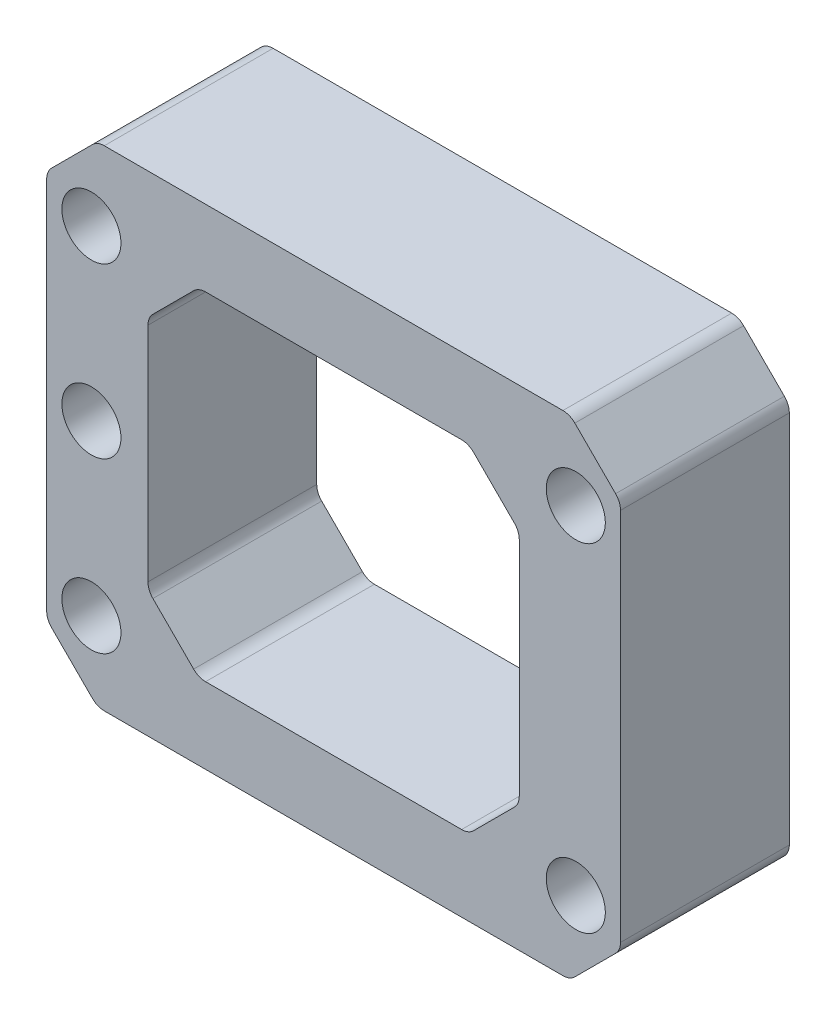
SolidWorks part; units mm, degrees
material "Thornel Mat VMA"
ref_plane "前视基准面" through (0, 0, 0) normal (0, 0, 1) x (1, 0, 0)
ref_plane "上视基准面" through (0, 0, 0) normal (0, 1, 0) x (1, 0, 0)
ref_plane "右视基准面" through (0, 0, 0) normal (1, 0, 0) x (0, 0, -1)
sketch "草图1" plane through (0, 0, 0) normal (0, 0, 1) x (1, 0, 0)
  line L1 (-17, 14.5) -> (17, 14.5)
  line L2 (-17, 14.5) -> (-17, -14.5)
  line L3 (-17, -14.5) -> (17, -14.5)
  line L4 (17, 14.5) -> (17, -14.5)
  line L5 (-17, 14.5) -> (17, -14.5) construction
  line L6 (-17, -14.5) -> (17, 14.5) construction
  line L7 (-14.35, 10) -> (14.35, 10) construction
  line L8 (-14.35, 10) -> (-14.35, -10) construction
  line L9 (-14.35, -10) -> (14.35, -10) construction
  line L10 (14.35, 10) -> (14.35, -10) construction
  line L11 (-14.35, 10) -> (14.35, -10) construction
  line L12 (-14.35, -10) -> (14.35, 10) construction
  circle A0 centre (-14.35, -10) radius 1.75
  circle A1 centre (-14.35, 10) radius 1.75
  circle A2 centre (14.35, 10) radius 1.75
  circle A3 centre (14.35, -10) radius 1.75
  circle A4 centre (-14.35, 0) radius 1.75
  point P0 (0, 0)
  point P6 (0, 0)
  dimension "D5" = 3.5
  dimension "D1" = 29
  dimension "D2" = 28.7
  dimension "D3" = 34
  dimension "D4" = 20
extrude "凸台-拉伸1" add sketch "草图1" along normal blind 10
chamfer "倒角1" distance 3 angle 45 4 edges at (17, -14.5, 5) (17, 14.5, 5) (-17, -14.5, 5) (-17, 14.5, 5)
sketch "草图2" plane through (0, 0, 10) normal (0, 0, 1) x (1, 0, 0)
  line L0 (-11, 7) -> (-8, 10)
  line L1 (-8, 10) -> (8, 10)
  line L2 (-11, 7) -> (-11, -7)
  line L3 (-8, -10) -> (8, -10)
  line L4 (11, 7) -> (11, -7)
  line L5 (-11, 10) -> (11, -10) construction
  line L6 (-11, -10) -> (11, 10) construction
  line L7 (8, 10) -> (11, 7)
  line L8 (-11, -7) -> (-8, -10)
  line L9 (8, -10) -> (11, -7)
  point P0 (0, 0)
  dimension "D1" = 22
  dimension "D2" = 20
extrude "切除-拉伸1" cut sketch "草图2" against normal through all
fillet "圆角1" radius 1 16 edges at (17, 11.5, 5) (14, 14.5, 5) (-14, 14.5, 5) (-17, 11.5, 5) (-17, -11.5, 5) (-14, -14.5, 5) (14, -14.5, 5) (17, -11.5, 5) (11, 7, 5) (11, -7, 5) (8, -10, 5) (-8, -10, 5) (-11, -7, 5) (-8, 10, 5) (8, 10, 5) (-11, 7, 5)
